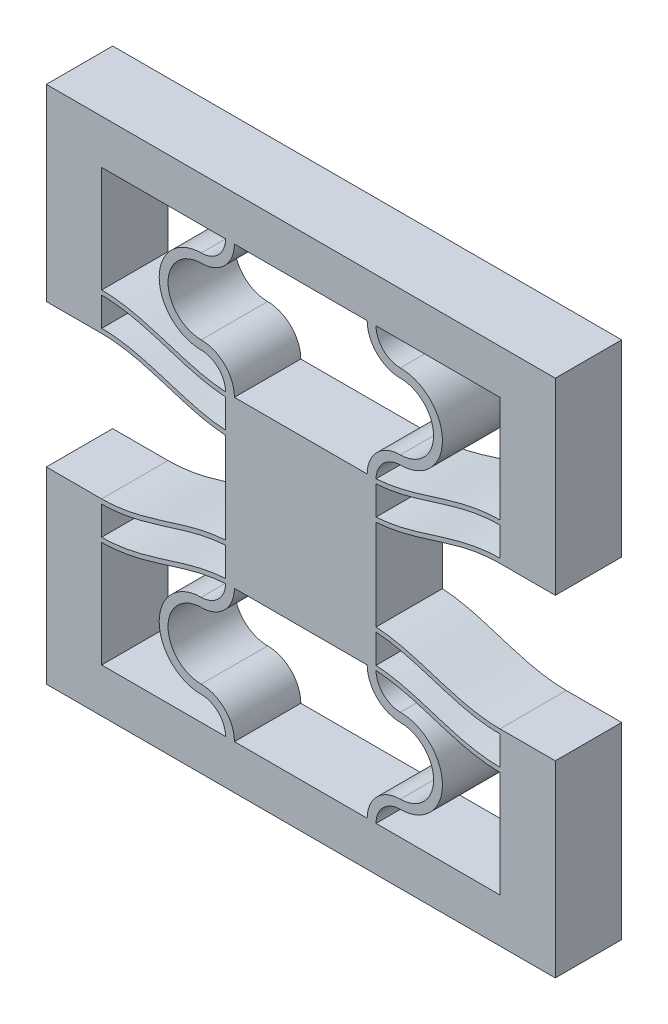
SolidWorks part; units mm, degrees
ref_plane "Front Plane" through (0, 0, 0) normal (0, 0, 1) x (1, 0, 0)
ref_plane "Top Plane" through (0, 0, 0) normal (0, 1, 0) x (1, 0, 0)
ref_plane "Right Plane" through (0, 0, 0) normal (1, 0, 0) x (0, 0, -1)
sketch "Sketch1" plane through (0, 0, 0) normal (0, 0, 1) x (1, 0, 0)
  line L4 (0, 9.6) -> (0, 0)
  line L5 (12, 0) -> (12, 12) construction
  line L6 (12, 12) -> (12, 17.9738) construction
  line L17 (11.2, 0) -> (0, 0)
  line L18 (12.8, 0) -> (24, 0)
  line L19 (24, 0) -> (24, 9.6)
  line L20 (12.8002, 12.3738) -> (12.8002, 14.9738)
  line L21 (11.1998, 12.3738) -> (11.1998, 14.9738)
  line L22 (12.8002, 15.3738) -> (12.8002, 17.9738)
  line L23 (12.8002, 17.9738) -> (11.1998, 17.9738)
  line L24 (11.1998, 17.9738) -> (11.1998, 15.3738)
  line L31 (-5, 13) -> (-5, -4)
  line L32 (-5, -4) -> (29, -4)
  line L33 (29, -4) -> (29, 13)
  line L34 (0, 10) -> (0, 12.6)
  line L35 (24, 10) -> (24, 12.6)
  line L36 (-5, 13) -> (0, 13)
  line L37 (29, 13) -> (24, 13)
  arc A0 (12, 12) -> (9, 9) centre (9, 12) cw
  arc A1 (9, 9) -> (9, 3) centre (9, 6) ccw
  arc A2 (9, 3) -> (12, 0) centre (9, 0) cw
  arc A3 (11.1998, 11.9738) -> (9, 9.8) centre (9, 12) cw
  arc A4 (9, 9.8) -> (9, 2.2) centre (9, 6) ccw
  arc A5 (9, 2.2) -> (11.2, 0) centre (9, 0) cw
  arc A6 (11.2, 12) -> (9, 9.8) centre (9, 12) cw construction
  arc A7 (15, 3) -> (12, 0) centre (15, 0) ccw
  arc A8 (15, 2.2) -> (12.8, 0) centre (15, 0) ccw
  arc A9 (15, 9) -> (15, 3) centre (15, 6) cw
  arc A10 (15, 9.8) -> (15, 2.2) centre (15, 6) cw
  arc A11 (12.8002, 11.9738) -> (15, 9.8) centre (15, 12) ccw
  arc A12 (12, 12) -> (15, 9) centre (15, 12) ccw
  spline S0 degree 4 poles (-2.3999, 10.2292) (-2.3254, 10.2154) (-2.1761, 10.1888) (-1.9504, 10.1518) (-1.6519, 10.1089) (-1.3471, 10.0727) (-1.0557, 10.0435) (-0.7362, 10.0215) (-0.4793, 10.0068) (-0.1104, 9.9998) (0.0567, 9.9993) (0.3491, 10.004) (0.5754, 10.0126) (0.8018, 10.0255) (1.0319, 10.0426) (1.2603, 10.0639) (1.4884, 10.0891) (1.7731, 10.1256) (2.1136, 10.1768) (2.5875, 10.2609) (3.1922, 10.39) (3.792, 10.5403) (4.3876, 10.7064) (4.904, 10.8595) (5.3429, 10.994) (6.1097, 11.2339) (7.1366, 11.5593) (8.2808, 11.8956) (9.5575, 12.1802) (10.6242, 12.3364) (11.5405, 12.4058) (12.4595, 12.4058) (13.3758, 12.3364) (14.4425, 12.1802) (15.495, 11.9456) (16.4224, 11.6872) (17.2334, 11.4402) (17.7811, 11.2689) (18.2189, 11.1311) (18.6571, 10.994) (19.0959, 10.8595) (19.6125, 10.7064) (20.2078, 10.5403) (20.9193, 10.3621) (21.6372, 10.2147) (22.2836, 10.1135) (22.796, 10.0565) (23.1411, 10.0288) (23.4248, 10.0126) (23.6508, 10.004) (23.9433, 9.9993) (24.1104, 9.9998) (24.4794, 10.0068) (24.7362, 10.0215) (25.0557, 10.0435) (25.3471, 10.0727) (25.6519, 10.1089) (25.9504, 10.1518) (26.1761, 10.1888) (26.3254, 10.2154) (26.3999, 10.2292) knots 0 0 0 0 0 0.010324 0.020648 0.030972 0.041296 0.051495 0.061694 0.071892 0.082091 0.089896 0.0977 0.105505 0.113309 0.121114 0.128918 0.136722 0.144527 0.160136 0.175745 0.202177 0.22861 0.244219 0.259828 0.275437 0.291046 0.353481 0.406346 0.437564 0.468782 0.5 0.531218 0.562436 0.593654 0.646519 0.677737 0.693345 0.708954 0.724563 0.740172 0.755781 0.77139 0.797823 0.824255 0.855473 0.871082 0.886691 0.894495 0.9023 0.910104 0.917909 0.928108 0.938306 0.948505 0.958704 0.969028 0.979352 0.989676 1 1 1 1 1 construction
  spline S1 degree 4 poles (0, 10) (0.048, 10) (0.1454, 10.0007) (0.3491, 10.004) (0.5754, 10.0126) (0.8018, 10.0255) (1.0319, 10.0426) (1.2603, 10.0639) (1.4884, 10.0891) (1.7731, 10.1256) (2.1136, 10.1768) (2.5875, 10.2609) (3.1922, 10.39) (3.792, 10.5403) (4.3876, 10.7064) (4.904, 10.8595) (5.3429, 10.994) (6.1097, 11.2339) (7.1366, 11.5593) (8.2808, 11.8956) (9.5575, 12.1802) (10.6242, 12.3364) (11.5405, 12.4058) (12.4595, 12.4058) (13.3758, 12.3364) (14.4425, 12.1802) (15.495, 11.9456) (16.4224, 11.6872) (17.2334, 11.4402) (17.7811, 11.2689) (18.2189, 11.1311) (18.6571, 10.994) (19.0959, 10.8595) (19.6125, 10.7064) (20.2078, 10.5403) (20.9193, 10.3621) (21.6372, 10.2147) (22.2836, 10.1135) (22.796, 10.0565) (23.1411, 10.0288) (23.4248, 10.0126) (23.6508, 10.004) (23.8546, 10.0007) (23.952, 10) (24, 10) knots 0.082091 0.082091 0.082091 0.082091 0.082091 0.089896 0.0977 0.105505 0.113309 0.121114 0.128918 0.136722 0.144527 0.160136 0.175745 0.202177 0.22861 0.244219 0.259828 0.275437 0.291046 0.353481 0.406346 0.437564 0.468782 0.5 0.531218 0.562436 0.593654 0.646519 0.677737 0.693345 0.708954 0.724563 0.740172 0.755781 0.77139 0.797823 0.824255 0.855473 0.871082 0.886691 0.894495 0.9023 0.910104 0.917909 0.917909 0.917909 0.917909 0.917909
  spline S2 degree 4 poles (-2.3999, 12.8292) (-2.3254, 12.8154) (-2.1761, 12.7888) (-1.9504, 12.7518) (-1.6519, 12.7089) (-1.3471, 12.6727) (-1.0557, 12.6435) (-0.7362, 12.6215) (-0.4793, 12.6068) (-0.1104, 12.5998) (0.0567, 12.5993) (0.3491, 12.604) (0.5754, 12.6126) (0.8018, 12.6255) (1.0319, 12.6426) (1.2603, 12.6639) (1.4884, 12.6891) (1.7731, 12.7256) (2.1136, 12.7768) (2.5875, 12.8609) (3.1922, 12.99) (3.792, 13.1403) (4.3876, 13.3064) (4.904, 13.4595) (5.3429, 13.594) (6.1097, 13.8339) (7.1366, 14.1593) (8.2808, 14.4956) (9.5575, 14.7802) (10.6242, 14.9364) (11.5405, 15.0058) (12.4595, 15.0058) (13.3758, 14.9364) (14.4425, 14.7802) (15.495, 14.5456) (16.4224, 14.2872) (17.2334, 14.0402) (17.7811, 13.8689) (18.2189, 13.7311) (18.6571, 13.594) (19.0959, 13.4595) (19.6125, 13.3064) (20.2078, 13.1403) (20.9193, 12.9621) (21.6372, 12.8147) (22.2836, 12.7135) (22.796, 12.6565) (23.1411, 12.6288) (23.4248, 12.6126) (23.6508, 12.604) (23.9433, 12.5993) (24.1104, 12.5998) (24.4794, 12.6068) (24.7362, 12.6215) (25.0557, 12.6435) (25.3471, 12.6727) (25.6519, 12.7089) (25.9504, 12.7518) (26.1761, 12.7888) (26.3254, 12.8154) (26.3999, 12.8292) knots 0 0 0 0 0 0.010324 0.020648 0.030972 0.041296 0.051495 0.061694 0.071892 0.082091 0.089896 0.0977 0.105505 0.113309 0.121114 0.128918 0.136722 0.144527 0.160136 0.175745 0.202177 0.22861 0.244219 0.259828 0.275437 0.291046 0.353481 0.406346 0.437564 0.468782 0.5 0.531218 0.562436 0.593654 0.646519 0.677737 0.693345 0.708954 0.724563 0.740172 0.755781 0.77139 0.797823 0.824255 0.855473 0.871082 0.886691 0.894495 0.9023 0.910104 0.917909 0.928108 0.938306 0.948505 0.958704 0.969028 0.979352 0.989676 1 1 1 1 1 construction
  spline S3 degree 4 poles (0, 12.6) (0.048, 12.6) (0.1454, 12.6007) (0.3491, 12.604) (0.5754, 12.6126) (0.8018, 12.6255) (1.0319, 12.6426) (1.2603, 12.6639) (1.4884, 12.6891) (1.7731, 12.7256) (2.1136, 12.7768) (2.5875, 12.8609) (3.1922, 12.99) (3.792, 13.1403) (4.3876, 13.3064) (4.904, 13.4595) (5.3429, 13.594) (6.1097, 13.8339) (7.1366, 14.1593) (8.2808, 14.4956) (9.5575, 14.7802) (10.6242, 14.9364) (11.5405, 15.0058) (12.4595, 15.0058) (13.3758, 14.9364) (14.4425, 14.7802) (15.495, 14.5456) (16.4224, 14.2872) (17.2334, 14.0402) (17.7811, 13.8689) (18.2189, 13.7311) (18.6571, 13.594) (19.0959, 13.4595) (19.6125, 13.3064) (20.2078, 13.1403) (20.9193, 12.9621) (21.6372, 12.8147) (22.2836, 12.7135) (22.796, 12.6565) (23.1411, 12.6288) (23.4248, 12.6126) (23.6508, 12.604) (23.8546, 12.6007) (23.952, 12.6) (24, 12.6) knots 0.082091 0.082091 0.082091 0.082091 0.082091 0.089896 0.0977 0.105505 0.113309 0.121114 0.128918 0.136722 0.144527 0.160136 0.175745 0.202177 0.22861 0.244219 0.259828 0.275437 0.291046 0.353481 0.406346 0.437564 0.468782 0.5 0.531218 0.562436 0.593654 0.646519 0.677737 0.693345 0.708954 0.724563 0.740172 0.755781 0.77139 0.797823 0.824255 0.855473 0.871082 0.886691 0.894495 0.9023 0.910104 0.917909 0.917909 0.917909 0.917909 0.917909
  spline S4 degree 4 poles (-2.3999, 13.2292) (-2.3254, 13.2154) (-2.1761, 13.1888) (-1.9504, 13.1518) (-1.6519, 13.1089) (-1.3471, 13.0727) (-1.0557, 13.0435) (-0.7362, 13.0215) (-0.4793, 13.0068) (-0.1104, 12.9998) (0.0567, 12.9993) (0.3491, 13.004) (0.5754, 13.0126) (0.8018, 13.0255) (1.0319, 13.0426) (1.2603, 13.0639) (1.4884, 13.0891) (1.7731, 13.1256) (2.1136, 13.1768) (2.5875, 13.2609) (3.1922, 13.39) (3.792, 13.5403) (4.3876, 13.7064) (4.904, 13.8595) (5.3429, 13.994) (6.1097, 14.2339) (7.1366, 14.5593) (8.2808, 14.8956) (9.5575, 15.1802) (10.6242, 15.3364) (11.5405, 15.4058) (12.4595, 15.4058) (13.3758, 15.3364) (14.4425, 15.1802) (15.495, 14.9456) (16.4224, 14.6872) (17.2334, 14.4402) (17.7811, 14.2689) (18.2189, 14.1311) (18.6571, 13.994) (19.0959, 13.8595) (19.6125, 13.7064) (20.2078, 13.5403) (20.9193, 13.3621) (21.6372, 13.2147) (22.2836, 13.1135) (22.796, 13.0565) (23.1411, 13.0288) (23.4248, 13.0126) (23.6508, 13.004) (23.9433, 12.9993) (24.1104, 12.9998) (24.4794, 13.0068) (24.7362, 13.0215) (25.0557, 13.0435) (25.3471, 13.0727) (25.6519, 13.1089) (25.9504, 13.1518) (26.1761, 13.1888) (26.3254, 13.2154) (26.3999, 13.2292) knots 0 0 0 0 0 0.010324 0.020648 0.030972 0.041296 0.051495 0.061694 0.071892 0.082091 0.089896 0.0977 0.105505 0.113309 0.121114 0.128918 0.136722 0.144527 0.160136 0.175745 0.202177 0.22861 0.244219 0.259828 0.275437 0.291046 0.353481 0.406346 0.437564 0.468782 0.5 0.531218 0.562436 0.593654 0.646519 0.677737 0.693345 0.708954 0.724563 0.740172 0.755781 0.77139 0.797823 0.824255 0.855473 0.871082 0.886691 0.894495 0.9023 0.910104 0.917909 0.928108 0.938306 0.948505 0.958704 0.969028 0.979352 0.989676 1 1 1 1 1 construction
  spline S5 degree 4 poles (0, 13) (0.048, 13) (0.1454, 13.0007) (0.3491, 13.004) (0.5754, 13.0126) (0.8018, 13.0255) (1.0319, 13.0426) (1.2603, 13.0639) (1.4884, 13.0891) (1.7731, 13.1256) (2.1136, 13.1768) (2.5875, 13.2609) (3.1922, 13.39) (3.792, 13.5403) (4.3876, 13.7064) (4.904, 13.8595) (5.3429, 13.994) (6.1097, 14.2339) (7.1366, 14.5593) (8.2808, 14.8956) (9.5575, 15.1802) (10.6242, 15.3364) (11.5405, 15.4058) (12.4595, 15.4058) (13.3758, 15.3364) (14.4425, 15.1802) (15.495, 14.9456) (16.4224, 14.6872) (17.2334, 14.4402) (17.7811, 14.2689) (18.2189, 14.1311) (18.6571, 13.994) (19.0959, 13.8595) (19.6125, 13.7064) (20.2078, 13.5403) (20.9193, 13.3621) (21.6372, 13.2147) (22.2836, 13.1135) (22.796, 13.0565) (23.1411, 13.0288) (23.4248, 13.0126) (23.6508, 13.004) (23.8546, 13.0007) (23.952, 13) (24, 13) knots 0.082091 0.082091 0.082091 0.082091 0.082091 0.089896 0.0977 0.105505 0.113309 0.121114 0.128918 0.136722 0.144527 0.160136 0.175745 0.202177 0.22861 0.244219 0.259828 0.275437 0.291046 0.353481 0.406346 0.437564 0.468782 0.5 0.531218 0.562436 0.593654 0.646519 0.677737 0.693345 0.708954 0.724563 0.740172 0.755781 0.77139 0.797823 0.824255 0.855473 0.871082 0.886691 0.894495 0.9023 0.910104 0.917909 0.917909 0.917909 0.917909 0.917909
  spline S6 degree 4 poles (-2.3999, 9.8292) (-2.3254, 9.8154) (-2.1761, 9.7888) (-1.9504, 9.7518) (-1.6519, 9.7089) (-1.3471, 9.6727) (-1.0557, 9.6435) (-0.7362, 9.6215) (-0.4793, 9.6068) (-0.1104, 9.5998) (0.0567, 9.5993) (0.3491, 9.604) (0.5754, 9.6126) (0.8018, 9.6255) (1.0319, 9.6426) (1.2603, 9.6639) (1.4884, 9.6891) (1.7731, 9.7256) (2.1136, 9.7768) (2.5875, 9.8609) (3.1922, 9.99) (3.792, 10.1403) (4.3876, 10.3064) (4.904, 10.4595) (5.3429, 10.594) (6.1097, 10.8339) (7.1366, 11.1593) (8.2808, 11.4956) (9.5575, 11.7802) (10.6242, 11.9364) (11.5405, 12.0058) (12.4595, 12.0058) (13.3758, 11.9364) (14.4425, 11.7802) (15.495, 11.5456) (16.4224, 11.2872) (17.2334, 11.0402) (17.7811, 10.8689) (18.2189, 10.7311) (18.6571, 10.594) (19.0959, 10.4595) (19.6125, 10.3064) (20.2078, 10.1403) (20.9193, 9.9621) (21.6372, 9.8147) (22.2836, 9.7135) (22.796, 9.6565) (23.1411, 9.6288) (23.4248, 9.6126) (23.6508, 9.604) (23.9433, 9.5993) (24.1104, 9.5998) (24.4794, 9.6068) (24.7362, 9.6215) (25.0557, 9.6435) (25.3471, 9.6727) (25.6519, 9.7089) (25.9504, 9.7518) (26.1761, 9.7888) (26.3254, 9.8154) (26.3999, 9.8292) knots 0 0 0 0 0 0.010324 0.020648 0.030972 0.041296 0.051495 0.061694 0.071892 0.082091 0.089896 0.0977 0.105505 0.113309 0.121114 0.128918 0.136722 0.144527 0.160136 0.175745 0.202177 0.22861 0.244219 0.259828 0.275437 0.291046 0.353481 0.406346 0.437564 0.468782 0.5 0.531218 0.562436 0.593654 0.646519 0.677737 0.693345 0.708954 0.724563 0.740172 0.755781 0.77139 0.797823 0.824255 0.855473 0.871082 0.886691 0.894495 0.9023 0.910104 0.917909 0.928108 0.938306 0.948505 0.958704 0.969028 0.979352 0.989676 1 1 1 1 1 construction
  spline S7 degree 4 poles (0, 9.6) (0.048, 9.6) (0.1454, 9.6007) (0.3491, 9.604) (0.5754, 9.6126) (0.8018, 9.6255) (1.0319, 9.6426) (1.2603, 9.6639) (1.4884, 9.6891) (1.7731, 9.7256) (2.1136, 9.7768) (2.5875, 9.8609) (3.1922, 9.99) (3.792, 10.1403) (4.3876, 10.3064) (4.904, 10.4595) (5.3429, 10.594) (6.1097, 10.8339) (7.1366, 11.1593) (8.2808, 11.4956) (9.5575, 11.7802) (10.6242, 11.9364) (11.5405, 12.0058) (12.4595, 12.0058) (13.3758, 11.9364) (14.4425, 11.7802) (15.495, 11.5456) (16.4224, 11.2872) (17.2334, 11.0402) (17.7811, 10.8689) (18.2189, 10.7311) (18.6571, 10.594) (19.0959, 10.4595) (19.6125, 10.3064) (20.2078, 10.1403) (20.9193, 9.9621) (21.6372, 9.8147) (22.2836, 9.7135) (22.796, 9.6565) (23.1411, 9.6288) (23.4248, 9.6126) (23.6508, 9.604) (23.8546, 9.6007) (23.952, 9.6) (24, 9.6) knots 0.082091 0.082091 0.082091 0.082091 0.082091 0.089896 0.0977 0.105505 0.113309 0.121114 0.128918 0.136722 0.144527 0.160136 0.175745 0.202177 0.22861 0.244219 0.259828 0.275437 0.291046 0.353481 0.406346 0.437564 0.468782 0.5 0.531218 0.562436 0.593654 0.646519 0.677737 0.693345 0.708954 0.724563 0.740172 0.755781 0.77139 0.797823 0.824255 0.855473 0.871082 0.886691 0.894495 0.9023 0.910104 0.917909 0.917909 0.917909 0.917909 0.917909
  point P22 (23.9721, 12.6394)
  point P23 (24, 13)
  point P24 (0, 0)
  point P25 (0, 0)
  point P28 (12.8002, 12.3738)
  point P32 (11.1998, 12.3738)
  point P34 (11.1998, 14.9738)
  point P35 (0, 0)
  point P37 (12.8002, 19.0136)
  point P46 (0, 0)
  point P47 (11.1998, 14.9738)
  point P48 (12.8002, 15.3738)
  point P50 (11.1998, 15.3738)
  dimension "D4" = 0.4
  dimension "D6" = 4
  dimension "D9" = 0.4
  dimension "D1" = 12
  dimension "D2" = 0.8
  dimension "D3" = 0.4
  dimension "D7" = 5
  dimension "D8" = 0.4
  dimension "D5" = 3
extrude "Boss-Extrude1" add sketch "Sketch1" along normal blind 2
sketch "Sketch4" plane through (0, 17.9738, 0) normal (0, 1, 0) x (1, 0, 0)
  line L24 (12.8002, 0) -> (11.1998, 0)
  line L25 (11.1998, 0) -> (11.1998, -2)
  line L26 (12.8002, 0) -> (11.1998, 0)
  line L27 (12.8002, -2) -> (12.8002, 0)
  line L29 (11.1998, 0) -> (11.1998, -2)
  line L31 (12.8002, -2) -> (12.8002, 0)
  line L32 (11.1998, -2) -> (12.8002, -2)
  line L33 (11.1998, -2) -> (12.8002, -2)
  dimension "D1" = 0
extrude "Boss-Extrude2" add sketch "Sketch4" along normal blind 1.5
mirror "Mirror3" about plane through (0, 19.4738, 0) normal (0, 1, 0) of bodies 179
ref_plane "Plane1" through (12, 0, 0) normal (-1, 0, 0) x (0, 0, 1)
split "Split2" trim tools "Plane1" bodies to split 247 102 resulting bodies 225
sketch "Sketch7" plane through (12, 0, 0) normal (-1, 0, 0) x (0, 0, 1)
  line L4 (2, 38.9475) -> (2, 42.9475)
  line L12 (0, 12) -> (2, 12)
  line L13 (0, 12) -> (2, 12)
  line L14 (2, 12) -> (2, 26.9475)
  line L15 (2, 12) -> (2, 26.9475)
  line L20 (2, 0) -> (0, 0)
  line L22 (2, 0) -> (0, 0)
  line L23 (0, -4) -> (2, -4)
  line L27 (0, -4) -> (2, -4)
  line L31 (2, 26.9475) -> (0, 26.9475)
  line L32 (2, 26.9475) -> (0, 26.9475)
  line L33 (0, 26.9475) -> (0, 12)
  line L34 (0, 26.9475) -> (0, 12)
  line L36 (2, -4) -> (2, 0)
  line L38 (2, 38.9475) -> (2, 42.9475)
  line L39 (2, 38.9475) -> (2, 42.9475)
  line L40 (2, 42.9475) -> (0, 42.9475)
  line L41 (2, 42.9475) -> (0, 42.9475)
  line L46 (2, 38.9475) -> (2, 42.9475)
  line L51 (0, 42.9475) -> (0, 38.9475)
  line L52 (0, 42.9475) -> (0, 38.9475)
  line L53 (0, 38.9475) -> (2, 38.9475)
  line L54 (0, 38.9475) -> (2, 38.9475)
  line L55 (2, 42.9475) -> (0, 42.9475)
  line L57 (2, 42.9475) -> (0, 42.9475)
  line L59 (2, -4) -> (2, 0)
  line L60 (0, 0) -> (0, -4)
  line L61 (0, 0) -> (0, -4)
  line L62 (0, 42.9475) -> (0, 38.9475)
  line L63 (0, 42.9475) -> (0, 38.9475)
  line L64 (0, 38.9475) -> (2, 38.9475)
  line L65 (0, 38.9475) -> (2, 38.9475)
  dimension "D1" = 0
  dimension "D2" = 0
  dimension "D3" = 0
  dimension "D4" = 0
extrude "Boss-Extrude3" add sketch "Sketch7" along normal blind 6
mirror "Mirror2" about plane through (6, 0, 0) normal (-1, 0, 0) of bodies 226
other "Move Face2" face at (6, 19.4738, 0) parameters "D1"=4
